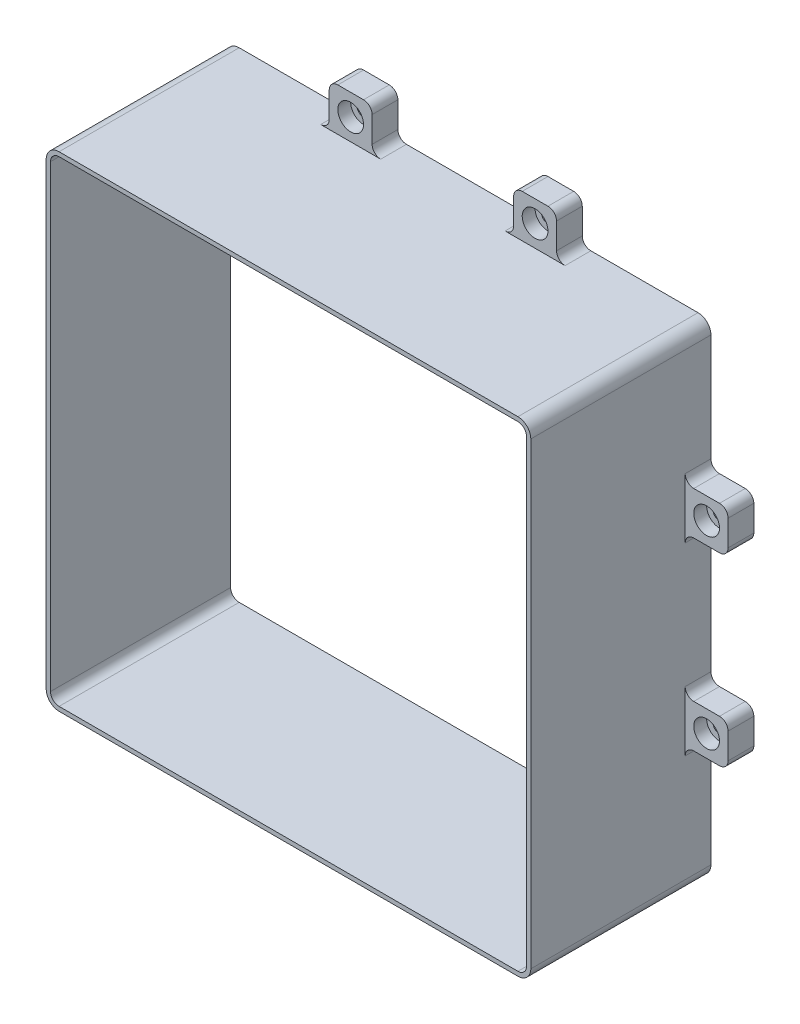
SolidWorks part; units mm, degrees
material "PMMA"
ref_plane "Přední rovina" through (0, 0, 0) normal (0, 0, 1) x (1, 0, 0)
ref_plane "Horní rovina" through (0, 0, 0) normal (0, 1, 0) x (1, 0, 0)
ref_plane "Pravá rovina" through (0, 0, 0) normal (1, 0, 0) x (0, 0, -1)
sketch "Skica2" plane through (0, 0, 0) normal (0, 0, 1) x (1, 0, 0)
  line L0 (1, -3) -> (1, -110)
  line L1 (3, 0) -> (110, 0)
  line L2 (0, -3) -> (0, -110)
  line L3 (3, -113) -> (110, -113)
  line L4 (113, -3) -> (113, -110)
  line L5 (3, -112) -> (110, -112)
  line L6 (112, -3) -> (112, -110)
  line L7 (3, -1) -> (110, -1)
  arc A0 (110, -113) -> (113, -110) centre (110, -110) ccw
  arc A1 (0, -110) -> (3, -113) centre (3, -110) ccw
  arc A2 (110, 0) -> (113, -3) centre (110, -3) cw
  arc A3 (3, 0) -> (0, -3) centre (3, -3) ccw
  arc A4 (1, -110) -> (3, -112) centre (3, -110) ccw
  arc A5 (110, -112) -> (112, -110) centre (110, -110) ccw
  arc A6 (110, -1) -> (112, -3) centre (110, -3) cw
  arc A7 (3, -1) -> (1, -3) centre (3, -3) ccw
  point P11 (113, 0)
  point P14 (0, 0)
  dimension "D2" = 3
  dimension "D1" = 113
  dimension "D3" = 1
extrude "Přidat vysunutím1" add sketch "Skica2" along normal blind 42 contours L2 A1 L3 A0 L4 A2 L1 A3 | L0 A4 L5 A5 L6 A6 L7 A7
ref_plane "Rovina1" through (56.5, 0, 0) normal (-1, 0, 0) x (0, 0, 1)
ref_plane "Rovina2" through (0, -56.5, 0) normal (0, 1, 0) x (1, 0, 0)
sketch "Skica7" plane through (0, 0, 0) normal (0, 1, 0) x (1, 0, 0)
  line L0 (3, 0) -> (110, 0) construction
  line L1 (30, 0) -> (40, 0)
  line L2 (30, 0) -> (30, -6)
  line L3 (30, -6) -> (40, -6)
  line L4 (40, 0) -> (40, -6)
  line L5 (0, -42) -> (0, 0) construction
  dimension "D1" = 10
  dimension "D2" = 30
  dimension "D3" = 6
extrude "Přidat vysunutím2" add sketch "Skica7" along normal blind 10
sketch "Skica6" plane through (56.5, 0, 0) normal (-1, 0, 0) x (0, 0, 1)
  line L0 (0, -56.5) -> (42, -56.5) construction
  line L1 (22, -56.5) -> (-22, -56.5) construction
  line L2 (42, -3) -> (42, -110) construction
  line L3 (0, -3) -> (0, -110) construction
sketch "Skica8" plane through (0, 0, 6) normal (0, 0, 1) x (1, 0, 0)
  line L0 (30, 10) -> (40, 0) construction
  circle A0 centre (35, 5) radius 3
  dimension "D1" = 6
extrude "Odebrat vysunutím4" cut sketch "Skica8" against normal blind 3
sketch "Skica9" plane through (0, 0, 3) normal (0, 0, 1) x (1, 0, 0)
  circle A0 centre (35, 5) radius 1.55
  circle A1 centre (35, 5) radius 3 construction
  dimension "D1" = 3.1
extrude "Odebrat vysunutím5" cut sketch "Skica9" against normal blind 3
pattern_linear "LinPole1" count 2 spacing 43 along (1, 0, 0) of "Přidat vysunutím2", "Odebrat vysunutím4", "Odebrat vysunutím5"
pattern_circular "Kruhové pole1" count 4 over 360 about axis through (56.5, -56.5, 0) along (0, 0, 1) of "Přidat vysunutím2", "Odebrat vysunutím4", "Odebrat vysunutím5", "LinPole1"
fillet "Zaoblit3" radius 2 32 edges at (83, -113, 3) (73, -113, 3) (83, -123, 3) (73, -123, 3) (0, -83, 3) (0, -73, 3) (-10, -83, 3) (-10, -73, 3) (113, -73, 3) (113, -83, 3) (123, -73, 3) (123, -83, 3) (40, -113, 3) (30, -113, 3) (40, -123, 3) (30, -123, 3) (0, -40, 3) (0, -30, 3) (-10, -40, 3) (-10, -30, 3) (30, 0, 3) (40, 0, 3) (30, 10, 3) (40, 10, 3) (73, 0, 3) (83, 0, 3) (73, 10, 3) (83, 10, 3) (113, -30, 3) (113, -40, 3) (123, -30, 3) (123, -40, 3)
